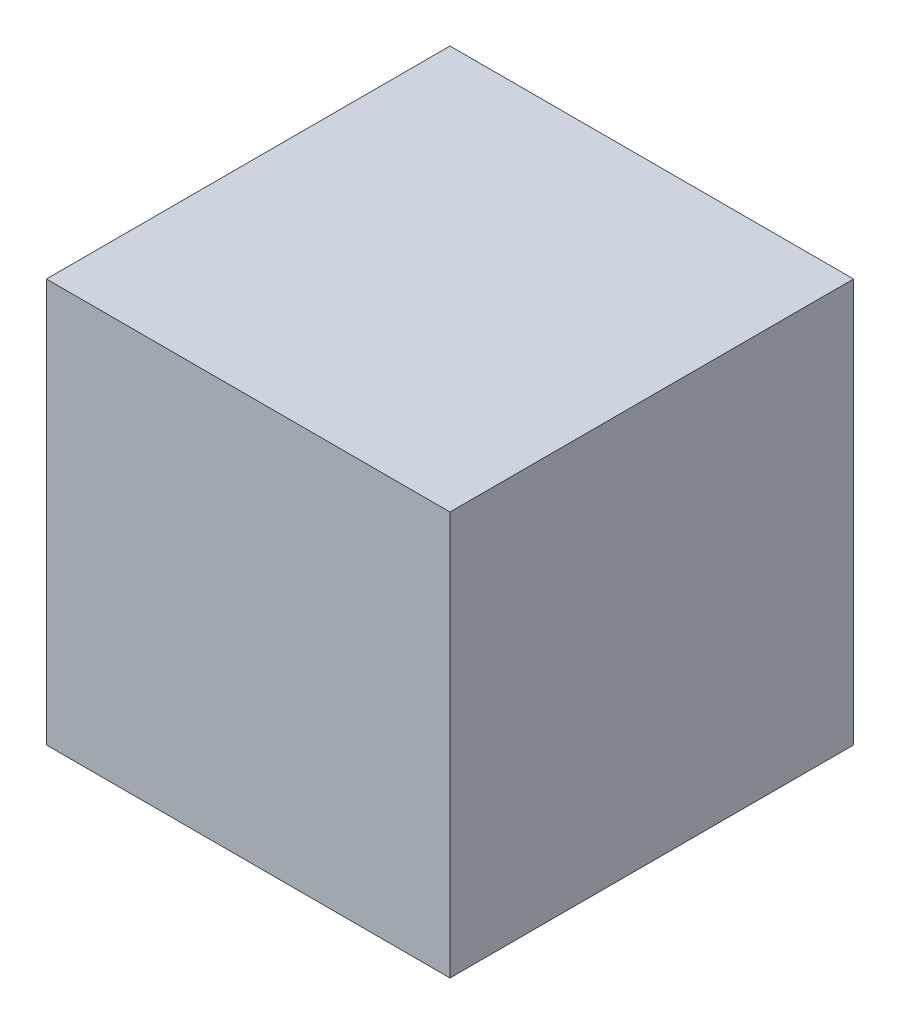
SolidWorks part; units mm, degrees
ref_plane "正面" through (0, 0, 0) normal (0, 0, 1) x (1, 0, 0)
ref_plane "平面" through (0, 0, 0) normal (0, 1, 0) x (1, 0, 0)
ref_plane "右側面" through (0, 0, 0) normal (1, 0, 0) x (0, 0, -1)
sketch "ｽｹｯﾁ1" plane through (0, 0, 0) normal (0, 0, 1) x (1, 0, 0)
  line L1 (0, 0) -> (900, 0)
  line L2 (0, 0) -> (0, 900)
  line L3 (0, 900) -> (900, 900)
  line L4 (900, 0) -> (900, 900)
  dimension "D1" = 900
  dimension "D2" = 900
extrude "ﾎﾞｽ - 押し出し1" add sketch "ｽｹｯﾁ1" along normal blind 900
